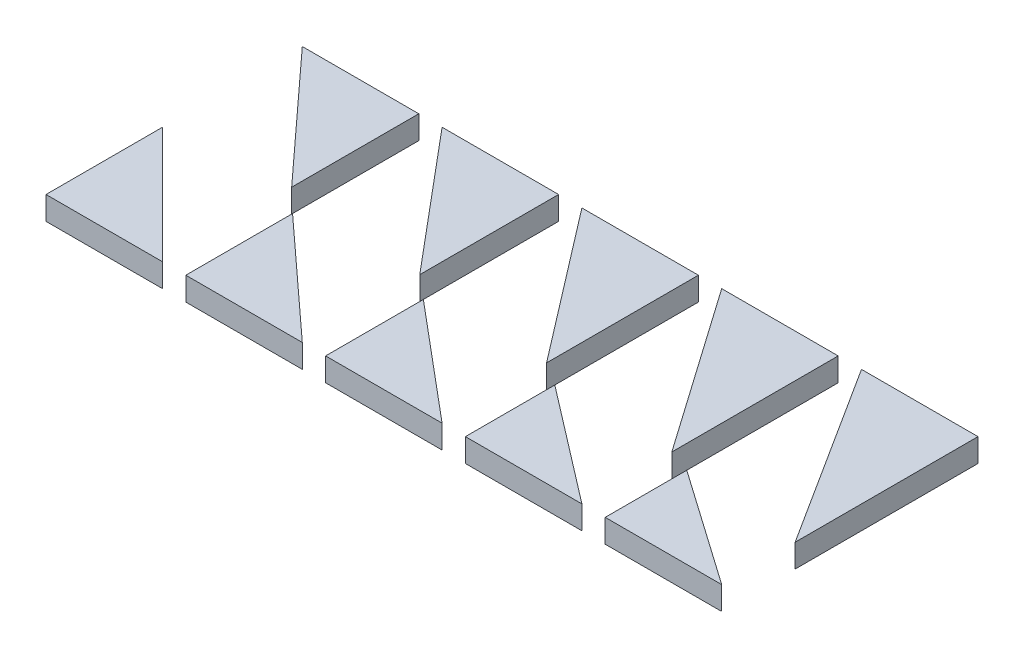
SolidWorks part; units mm, degrees
ref_plane "Front Plane" through (0, 0, 0) normal (0, 0, 1) x (1, 0, 0)
ref_plane "Top Plane" through (0, 0, 0) normal (0, 1, 0) x (1, 0, 0)
ref_plane "Right Plane" through (0, 0, 0) normal (1, 0, 0) x (0, 0, -1)
sketch "Sketch1" plane through (0, 0, 0) normal (0, 1, 0) x (1, 0, 0)
  line L0 (0, 0) -> (50, 0)
  line L1 (0, 0) -> (360, 0) construction
  line L2 (0, 0) -> (0, 110) construction
  line L3 (0, 110) -> (360, 110) construction
  line L4 (360, 0) -> (360, 110) construction
  line L5 (0, 0) -> (360, 110) construction
  line L6 (0, 110) -> (360, 0) construction
  line L7 (50, 0) -> (0, 50)
  line L8 (0, 50) -> (0, 0)
  line L9 (60, 0) -> (110, 0)
  line L10 (110, 0) -> (60, 45.8166)
  line L11 (60, 45.8166) -> (60, 0)
  line L12 (120, 0) -> (170, 0)
  line L13 (170, 0) -> (120, 41.955)
  line L14 (120, 41.955) -> (120, 0)
  line L15 (180, 0) -> (230, 0)
  line L16 (230, 0) -> (180, 38.3663)
  line L17 (180, 38.3663) -> (180, 0)
  line L18 (240, 0) -> (290, 0)
  line L19 (290, 0) -> (240, 35.0104)
  line L20 (240, 35.0104) -> (240, 0)
  line L21 (0, 110) -> (50, 55.4346)
  line L22 (50, 55.4346) -> (50, 110)
  line L23 (50, 110) -> (0, 110)
  line L24 (60, 110) -> (110, 50.4123)
  line L25 (110, 50.4123) -> (110, 110)
  line L26 (110, 110) -> (60, 110)
  line L27 (120, 110) -> (170, 44.8387)
  line L28 (170, 44.8387) -> (170, 110)
  line L30 (120, 110) -> (180, 110)
  line L31 (180, 110) -> (230, 38.5926)
  line L32 (230, 38.5926) -> (230, 110)
  line L33 (230, 110) -> (180, 110)
  line L34 (240, 110) -> (290, 31.5157)
  line L35 (290, 31.5157) -> (290, 110)
  line L36 (290, 110) -> (240, 110)
  point P4 (180, 55)
  dimension "D1" = 110
  dimension "D2" = 360
  dimension "D3" = 50
  dimension "D4" = 10
  dimension "D5" = 10
  dimension "D6" = 10
  dimension "D7" = 10
  dimension "D8" = 10
  dimension "D9" = 10
  dimension "D10" = 10
  dimension "D11" = 10
  dimension "D12" = 45
  dimension "D13" = 47.5
  dimension "D14" = 50
  dimension "D15" = 52.5
  dimension "D16" = 55
  dimension "D17" = 42.5
  dimension "D18" = 40
  dimension "D19" = 37.5
  dimension "D20" = 35
  dimension "D21" = 32.5
extrude "Boss-Extrude1" add sketch "Sketch1" along normal blind 10
